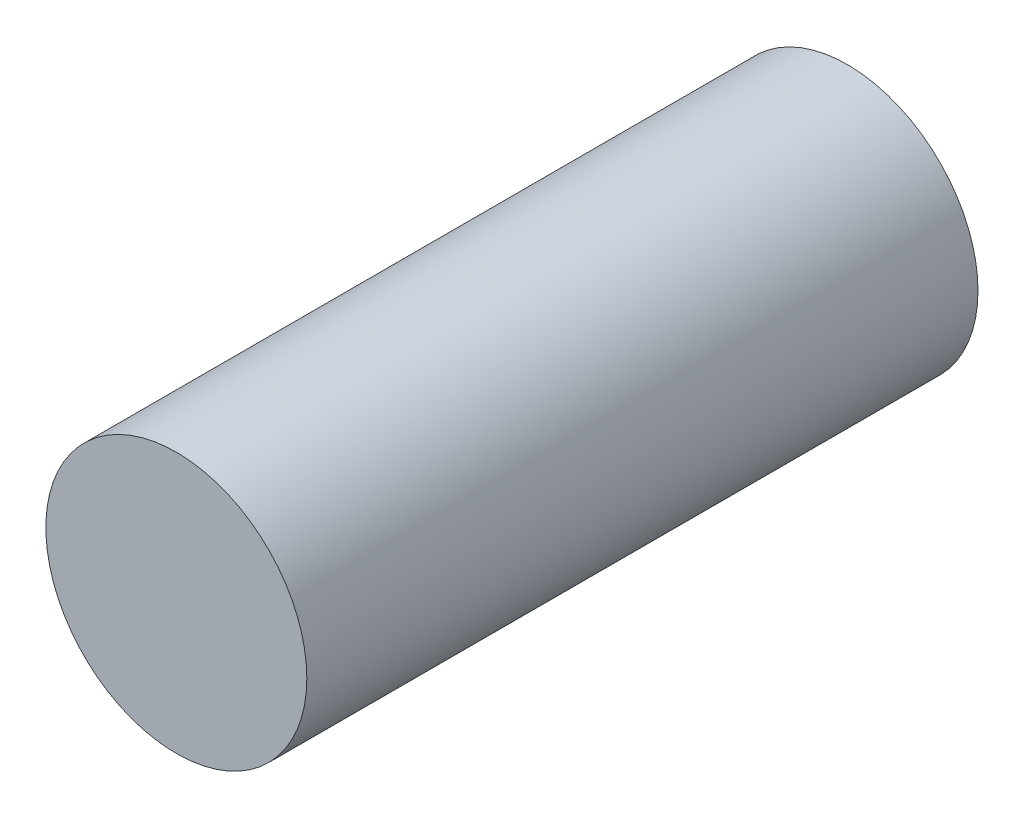
SolidWorks part; units mm, degrees
ref_plane "Front Plane" through (0, 0, 0) normal (0, 0, 1) x (1, 0, 0)
ref_plane "Top Plane" through (0, 0, 0) normal (0, 1, 0) x (1, 0, 0)
ref_plane "Right Plane" through (0, 0, 0) normal (1, 0, 0) x (0, 0, -1)
sketch "Sketch1" plane through (0, 0, 0) normal (0, 0, 1) x (1, 0, 0)
  circle A0 centre (0, 0) radius 4
extrude "Boss-Extrude1" add sketch "Sketch1" along normal blind 20.574
